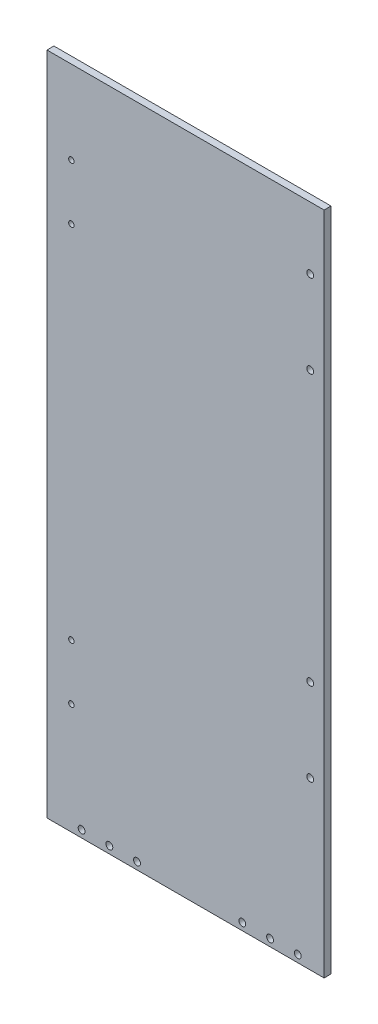
SolidWorks part; units mm, degrees
material "PC High Viscosity"
ref_plane "Front Plane" through (0, 0, 0) normal (0, 0, 1) x (1, 0, 0)
ref_plane "Top Plane" through (0, 0, 0) normal (0, 1, 0) x (1, 0, 0)
ref_plane "Right Plane" through (0, 0, 0) normal (1, 0, 0) x (0, 0, -1)
sketch "Sketch1" plane through (0, 0, 0) normal (0, 0, 1) x (1, 0, 0)
  line L1 (0, -234.4615) -> (-254, -234.4615)
  line L2 (0, -234.4615) -> (0, -844.0615)
  line L3 (0, -844.0615) -> (-254, -844.0615)
  line L4 (-254, -234.4615) -> (-254, -844.0615)
  dimension "D1" = 609.6
  dimension "D2" = 254
extrude "Boss-Extrude1" add sketch "Sketch1" along normal blind 6.35 contours L4 L3 L2 L1
sketch "Sketch2" plane through (0, 0, 6.35) normal (0, 0, 1) x (1, 0, 0)
  line L0 (-254, -234.4615) -> (-254, -844.0615) construction
  line L1 (0, -234.4615) -> (-254, -234.4615) construction
  circle A0 centre (-231.648, -310.6615) radius 2.4638
  circle A1 centre (-231.648, -361.4615) radius 2.4638
  circle A2 centre (-231.648, -691.6615) radius 2.4638
  circle A3 centre (-231.648, -742.4615) radius 2.4638
  dimension "D5" = 4.9276
  dimension "D1" = 22.352
  dimension "D2" = 50.8
  dimension "D3" = 330.2
  dimension "D4" = 50.8
  dimension "D6" = 76.2
extrude "Cut-Extrude1" cut sketch "Sketch2" against normal through all
sketch "Sketch3" plane through (0, 0, 0) normal (0, 0, -1) x (-1, 0, 0)
  line L0 (0, -234.4615) -> (0, -844.0615) construction
  line L1 (0, -844.0615) -> (254, -844.0615) construction
  line L2 (254, -234.4615) -> (254, -844.0615) construction
  circle A0 centre (24.13, -837.4575) radius 3.175
  circle A1 centre (49.53, -837.4575) radius 3.175
  circle A2 centre (74.9916, -837.4575) radius 3.175
  circle A3 centre (196.85, -837.4575) radius 3.175
  circle A4 centre (171.45, -837.4575) radius 3.175
  circle A5 centre (222.25, -837.4575) radius 3.175
  dimension "D3" = 6.35
  dimension "D5" = 25.4
  dimension "D1" = 31.75
  dimension "D2" = 6.604
  dimension "D4" = 25.4
  dimension "D6" = 25.4616
  dimension "D7" = 25.4
  dimension "D8" = 24.13
extrude "Cut-Extrude2" cut sketch "Sketch3" against normal blind 6.35
sketch "Sketch4" plane through (0, 0, 6.35) normal (0, 0, 1) x (1, 0, 0)
  line L0 (0, -234.4615) -> (-254, -234.4615) construction
  line L1 (0, -234.4615) -> (0, -844.0615) construction
  line L2 (0, -844.0615) -> (-254, -844.0615) construction
  line L4 (0, -234.4615) -> (0, -844.0615) construction
  circle A0 centre (-12.7, -291.6115) radius 3.175
  circle A1 centre (-12.7, -367.8115) radius 3.175
  circle A2 centre (-12.7, -691.6615) radius 3.175
  circle A3 centre (-12.7, -615.4615) radius 3.175
  dimension "D2" = 6.35
  dimension "D7" = 6.35
  dimension "D8" = 6.35
  dimension "D1" = 76.2
  dimension "D3" = 57.15
  dimension "D4" = 12.7
  dimension "D5" = 76.2
  dimension "D6" = 152.4
  dimension "D9" = 12.7
extrude "Cut-Extrude3" cut sketch "Sketch4" against normal blind 6.35
